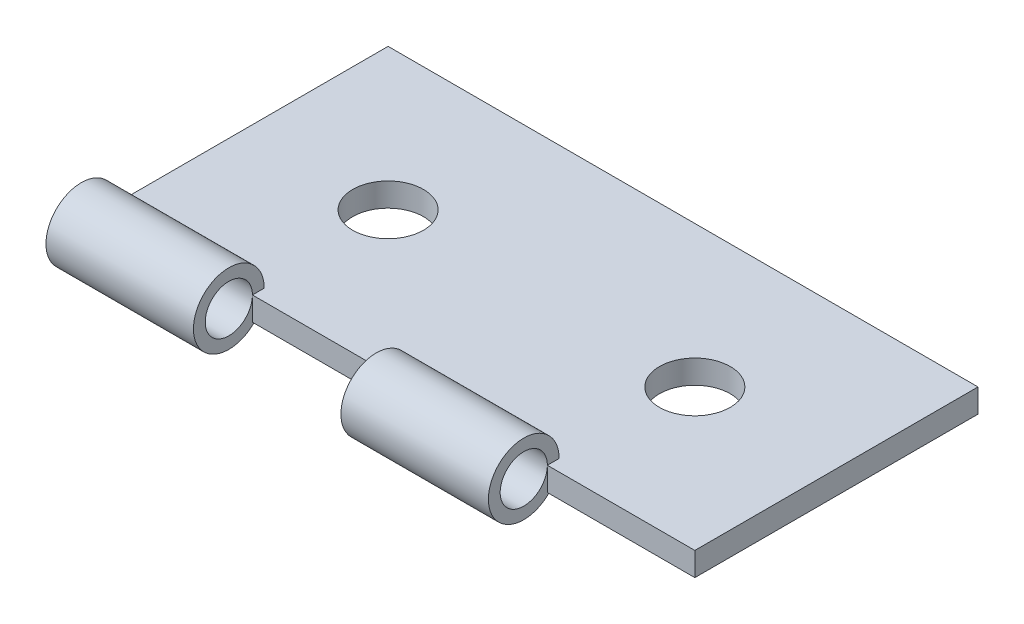
SolidWorks part; units mm, degrees
ref_plane "Front Plane" through (0, 0, 0) normal (0, 0, 1) x (1, 0, 0)
ref_plane "Top Plane" through (0, 0, 0) normal (0, 1, 0) x (1, 0, 0)
ref_plane "Right Plane" through (0, 0, 0) normal (1, 0, 0) x (0, 0, -1)
sketch "Sketch1" plane through (0, 0, 0) normal (0, 1, 0) x (1, 0, 0)
  line L0 (0, 6) -> (24.5423, 6) construction
  line L1 (0, 0) -> (25, 0)
  line L2 (0, 0) -> (0, 12)
  line L3 (0, 12) -> (25, 12)
  line L4 (25, 0) -> (25, 12)
  circle A0 centre (6, 6) radius 1.5
  circle A1 centre (19, 6) radius 1.5
  point P9 (25, 6)
  dimension "D3" = 3
  dimension "D4" = 3
  dimension "D1" = 25
  dimension "D2" = 12
  dimension "D5" = 6
  dimension "D6" = 6
extrude "Boss-Extrude1" add sketch "Sketch1" along normal blind 1
sketch "Sketch2" plane through (0, 0, 0) normal (1, 0, 0) x (0, 0, -1)
  line L0 (0, 1) -> (-3.5021, 1) construction
  circle A0 centre (-1, 1) radius 1.5
  circle A2 centre (-1, 1) radius 1
  dimension "D1" = 3
  dimension "D2" = 0
  dimension "D4" = 2
extrude "Boss-Extrude2" add sketch "Sketch2" along direction (1, 0, 0) on the side of the normal offset from surface (6.25 mm away) 6.25
sketch "Sketch3" plane through (0, 0, 0) normal (1, 0, 0) x (0, 0, -1)
  line L0 (-0.1458, 1.5199) -> (-1.1812, 0.8897) construction
  circle A0 centre (-1, 1) radius 1.5
  circle A1 centre (-1, 1) radius 1
  dimension "D1" = 2
  dimension "D2" = 3
extrude "Boss-Extrude3" add sketch "Sketch3" along normal blind 6.25 from offset 12.5
